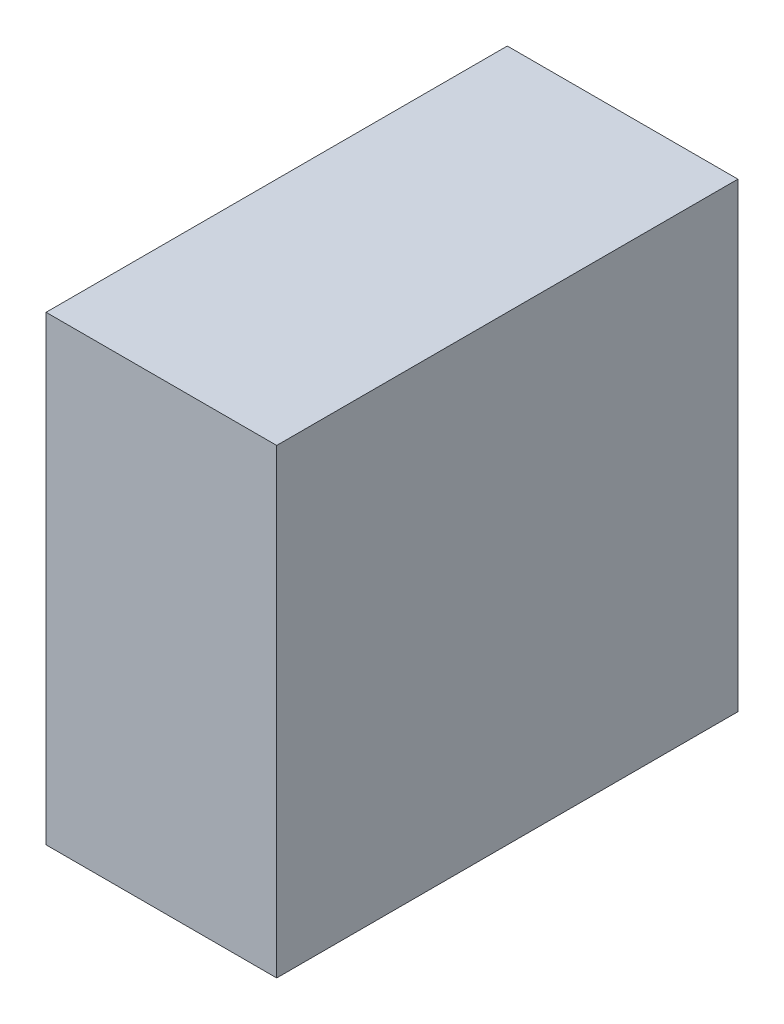
SolidWorks part; units mm, degrees
ref_plane "Front Plane" through (0, 0, 0) normal (0, 0, 1) x (1, 0, 0)
ref_plane "Top Plane" through (0, 0, 0) normal (0, 1, 0) x (1, 0, 0)
ref_plane "Right Plane" through (0, 0, 0) normal (1, 0, 0) x (0, 0, -1)
sketch "Sketch1" plane through (0, 0, 0) normal (0, 0, 1) x (1, 0, 0)
  line L1 (0, 0) -> (40, 0)
  line L2 (0, 0) -> (0, 40)
  line L3 (0, 40) -> (40, 40)
  line L4 (40, 0) -> (40, 40)
  dimension "D1" = 40
  dimension "D2" = 40
extrude "Boss-Extrude1" add sketch "Sketch1" along normal blind 40
sketch "Sketch2" plane through (0, 0, 40) normal (0, 0, 1) x (1, 0, 0)
  line L0 (0, 0) -> (20, 40)
  line L1 (40, 40) -> (0, 40) construction
  line L2 (20, 40) -> (0, 40)
  line L3 (0, 40) -> (0, 0)
extrude "Cut-Extrude1" cut sketch "Sketch2" against normal blind 40
sketch "Sketch3" plane through (0, 0, 0) normal (0, -1, 0) x (-1, 0, 0)
  line L1 (0, -40) -> (-20, -40)
  line L2 (0, -40) -> (0, -20)
  line L3 (0, -20) -> (-20, -20)
  line L4 (-20, -40) -> (-20, -20)
  dimension "D1" = 20
  dimension "D2" = 20
extrude "Cut-Extrude2" cut sketch "Sketch3" against normal blind 40
sketch "Sketch4" plane through (0, 0, 0) normal (0, -1, 0) x (1, 0, 0)
  line L0 (0, 20) -> (20, 0)
  line L1 (0, 0) -> (40, 0) construction
  line L2 (20, 0) -> (0, 0)
  line L3 (0, 0) -> (0, 20)
  line L4 (0, 20) -> (-0.0692, 19.7637)
  line M4 (0, 20) -> (0, 0)
  line M5 (0, 0) -> (40, 0)
extrude "Cut-Extrude3" cut sketch "Sketch4" against normal blind 40 contours L0 M4 M5
